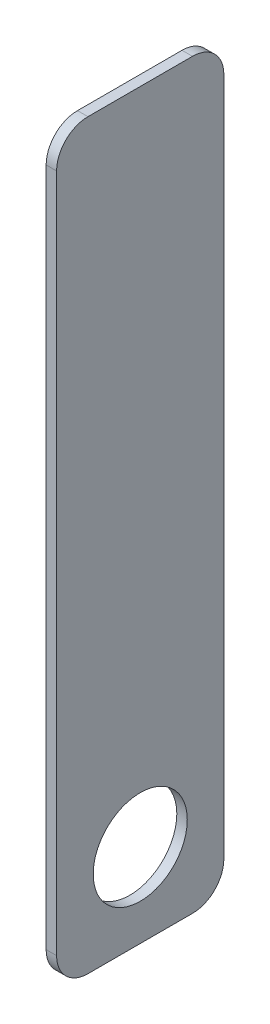
SolidWorks part; units mm, degrees
material "6063-O"
ref_plane "Front" through (0, 0, 0) normal (0, 0, 1) x (1, 0, 0)
ref_plane "Top" through (0, 0, 0) normal (0, 1, 0) x (1, 0, 0)
ref_plane "Right" through (0, 0, 0) normal (1, 0, 0) x (0, 0, -1)
sketch "Sketch1" plane through (0, 0, 0) normal (1, 0, 0) x (0, 0, -1)
  line L0 (0, 112.7125) -> (0, -112.7125) construction
  line L1 (-25.4, 112.7125) -> (25.4, 112.7125)
  line L2 (-25.4, 112.7125) -> (-25.4, -112.7125)
  line L3 (-25.4, -112.7125) -> (25.4, -112.7125)
  line L4 (25.4, 112.7125) -> (25.4, -112.7125)
  circle A0 centre (0, -87.3125) radius 14.2875
  point P4 (0, 0)
  dimension "D3" = 28.575
  dimension "D1" = 50.8
  dimension "D2" = 225.425
  dimension "D4" = 25.4
extrude "Boss-Extrude1" add sketch "Sketch1" along normal blind 3.175
fillet "Fillet1" radius 9.525 4 edges at (1.5875, -112.7125, -25.4) (1.5875, -112.7125, 25.4) (1.5875, 112.7125, -25.4) (1.5875, 112.7125, 25.4)
